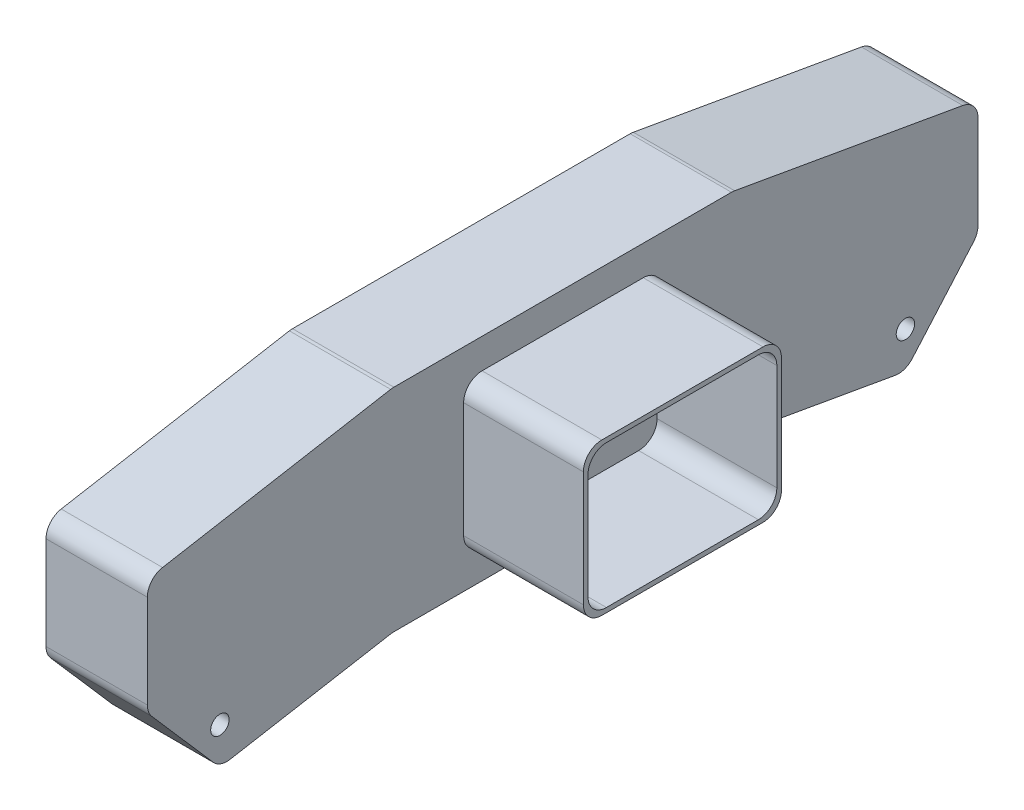
SolidWorks part; units mm, degrees
ref_plane "Front Plane" through (0, 0, 0) normal (0, 0, 1) x (1, 0, 0)
ref_plane "Top Plane" through (0, 0, 0) normal (0, 1, 0) x (1, 0, 0)
ref_plane "Right Plane" through (0, 0, 0) normal (1, 0, 0) x (0, 0, -1)
sketch "Sketch1" plane through (0, 0, 0) normal (1, 0, 0) x (0, 0, -1)
  line L0 (-21.7455, 8.298) -> (-48.3353, 3.6095)
  line L1 (-21.7455, 8.298) -> (15.2545, 8.298)
  line L2 (-3.2455, 8.298) -> (-3.2455, -3.6062) construction
  line L3 (-21.7455, -14.702) -> (15.2545, -14.702)
  line L4 (41.8443, 3.6095) -> (41.8443, -8.9498)
  line L5 (41.8443, -8.9498) -> (33.9658, -18.0013)
  line L6 (15.2545, -14.702) -> (33.9658, -18.0013)
  line L7 (-21.7455, -14.702) -> (-40.4569, -18.0013)
  line L8 (-48.3353, -8.9498) -> (-40.4569, -18.0013)
  line L9 (-48.3353, 3.6095) -> (-48.3353, -8.9498)
  line L10 (15.2545, 8.298) -> (41.8443, 3.6095)
  circle A0 centre (-40.4569, -14.0013) radius 1
  circle A1 centre (33.9658, -14.0013) radius 1
  dimension "D8" = 2
  dimension "D1" = 37
  dimension "D2" = 23
  dimension "D3" = 27
  dimension "D4" = 12
  dimension "D5" = 19
  dimension "D6" = 190
  dimension "D7" = 12.5593
  dimension "D9" = 4
  dimension "D10" = 37
extrude "Boss-Extrude1" add sketch "Sketch1" along normal blind 11
sketch "Sketch2" plane through (11, 0, 0) normal (1, 0, 0) x (0, 0, -1)
  line L0 (-3.2455, 8.298) -> (-3.2455, -14.702) construction
  line L1 (15.2545, 8.298) -> (-21.7455, 8.298) construction
  line L2 (-21.7455, -14.702) -> (15.2545, -14.702) construction
  line L3 (-3.2455, -3.202) -> (6.4629, -3.202) construction
  line L5 (-13.7455, 4.798) -> (7.2545, 4.798)
  line L6 (-13.7455, 4.798) -> (-13.7455, -11.202)
  line L7 (-13.7455, -11.202) -> (7.2545, -11.202)
  line L8 (7.2545, 4.798) -> (7.2545, -11.202)
  line L9 (-13.7455, 4.798) -> (7.2545, -11.202) construction
  line L10 (-13.7455, -11.202) -> (7.2545, 4.798) construction
  dimension "D1" = 16
  dimension "D2" = 21
extrude "Extrude-Thin1" add sketch "Sketch2" along normal blind 13 thin thin type mid plane wall 0.5
fillet "Fillet1" radius 2 10 edges at (5.5, -14.702, 21.7455) (5.5, -14.702, -15.2545) (5.5, -18.0013, -33.9658) (5.5, -8.9498, -41.8443) (5.5, 3.6095, -41.8443) (5.5, 8.298, -15.2545) (5.5, -18.0013, 40.4569) (5.5, -8.9498, 48.3353) (5.5, 3.6095, 48.3353) (5.5, 8.298, 21.7455)
fillet "Fillet2" radius 2 8 edges at (17.5, 4.548, -7.0045) (17.5, -10.952, -7.0045) (17.5, -10.952, 13.4955) (17.5, 4.548, 13.4955) (17.5, -11.452, -7.5045) (17.5, -11.452, 13.9955) (17.5, 5.048, -7.5045) (17.5, 5.048, 13.9955)
